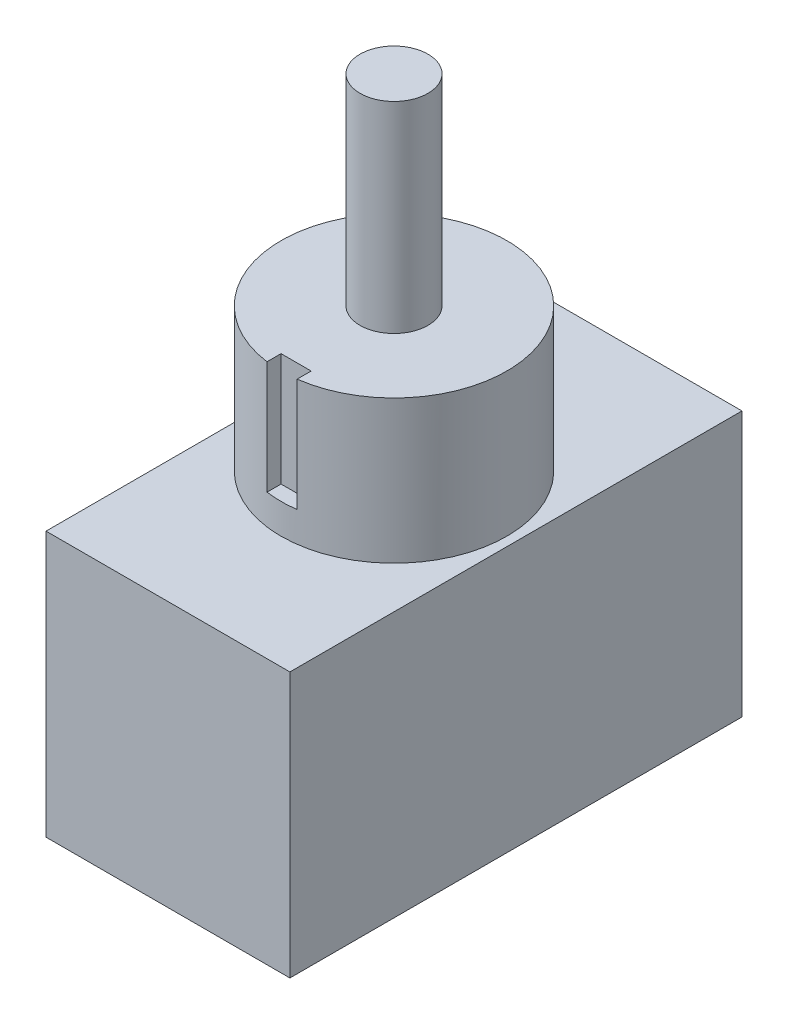
SolidWorks part; units mm, degrees
ref_plane "Front Plane" through (0, 0, 0) normal (0, 0, 1) x (1, 0, 0)
ref_plane "Top Plane" through (0, 0, 0) normal (0, 1, 0) x (1, 0, 0)
ref_plane "Right Plane" through (0, 0, 0) normal (1, 0, 0) x (0, 0, -1)
sketch "Sketch1" plane through (0, 0, 0) normal (0, 1, 0) x (1, 0, 0)
  line L1 (-14.8395, 10.2472) -> (-1.9871, 10.2472)
  line L2 (-14.8395, 10.2472) -> (-14.8395, -13.578)
  line L3 (-14.8395, -13.578) -> (-1.9871, -13.578)
  line L4 (-1.9871, 10.2472) -> (-1.9871, -13.578)
  dimension "D1" = 12.8524
  dimension "D2" = 23.8252
extrude "Boss-Extrude1" add sketch "Sketch1" along normal blind 13.97
sketch "Sketch2" plane through (0, 13.97, 0) normal (0, 1, 0) x (1, 0, 0)
  line L0 (-1.9871, -13.578) -> (-1.9871, 10.2472) construction
  line L1 (-1.9871, 10.2472) -> (-14.8395, 10.2472) construction
  circle A0 centre (-8.4133, -1.6654) radius 5.9531
  point P5 (-1.9871, -1.6654)
  point P8 (-8.4133, 10.2472)
  dimension "D1" = 11.9062
extrude "Boss-Extrude2" add sketch "Sketch2" along normal blind 7.5406
sketch "Sketch3" plane through (0, 21.5106, 0) normal (0, 1, 0) x (1, 0, 0)
  line L1 (-9.2071, -6.8248) -> (-7.6196, -6.8248)
  line L2 (-9.2071, -6.8248) -> (-9.2071, -7.6185)
  line L3 (-9.2071, -7.6185) -> (-7.6196, -7.6185)
  line L4 (-7.6196, -6.8248) -> (-7.6196, -7.6185)
  circle A0 centre (-8.4133, -1.6654) radius 5.9531 construction
  circle A1 centre (-8.4133, -1.6654) radius 5.9531 construction
  point P10 (-8.4133, -7.6185)
  dimension "D1" = 1.5875
  dimension "D2" = 0.7937
extrude "Cut-Extrude1" cut sketch "Sketch3" against normal offset from surface (5.9531 mm away) 1.5875 up to face at (-8.4133, 13.97, 7.6185)
sketch "Sketch4" plane through (0, 21.5106, 0) normal (0, 1, 0) x (1, 0, 0)
  circle A0 centre (-8.4133, -1.6654) radius 1.7906
extrude "Boss-Extrude3" add sketch "Sketch4" along normal blind 10.5918
